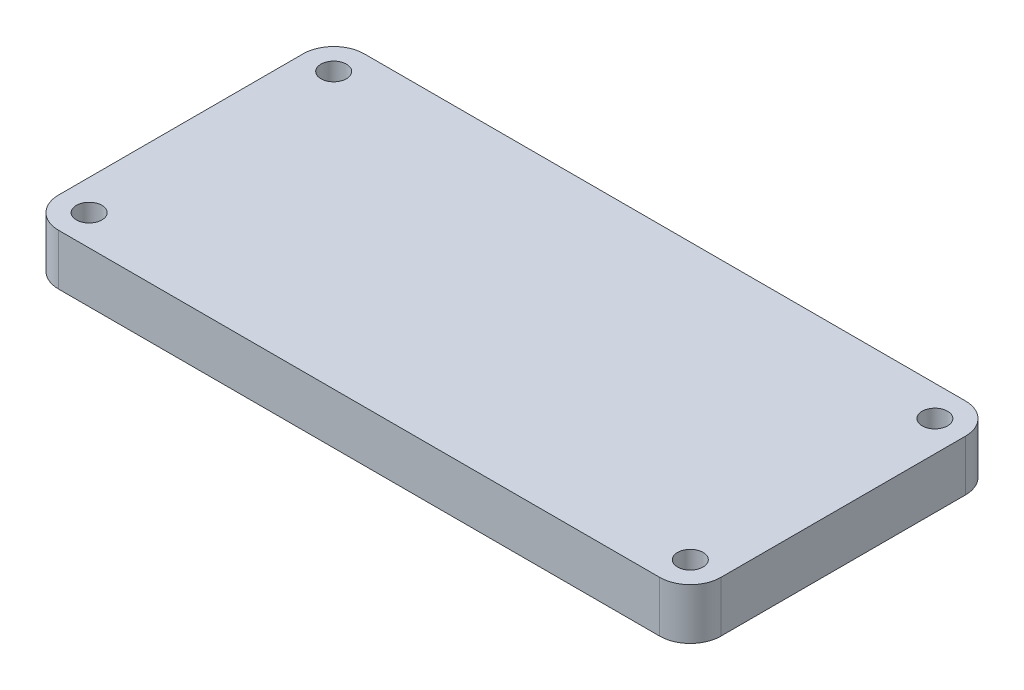
SolidWorks part; units mm, degrees
ref_plane "Front Plane" through (0, 0, 0) normal (0, 0, 1) x (1, 0, 0)
ref_plane "Top Plane" through (0, 0, 0) normal (0, 1, 0) x (1, 0, 0)
ref_plane "Right Plane" through (0, 0, 0) normal (1, 0, 0) x (0, 0, -1)
sketch "Sketch1" plane through (0, 0, 0) normal (0, 1, 0) x (1, 0, 0)
  line L0 (0, 15) -> (0, -15) construction
  line L1 (-29.5, -15) -> (29.5, -15)
  line L2 (-32.5, -12) -> (-32.5, 12)
  line L3 (-29.5, 15) -> (29.5, 15)
  line L4 (32.5, -12) -> (32.5, 12)
  line L5 (-32.5, -15) -> (32.5, 15) construction
  line L6 (-32.5, 15) -> (32.5, -15) construction
  line L7 (-32.5, 0) -> (32.5, 0) construction
  arc A0 (29.5, 15) -> (32.5, 12) centre (29.5, 12) cw
  arc A1 (32.5, -12) -> (29.5, -15) centre (29.5, -12) cw
  arc A2 (-29.5, -15) -> (-32.5, -12) centre (-29.5, -12) cw
  arc A3 (-32.5, 12) -> (-29.5, 15) centre (-29.5, 12) cw
  circle A4 centre (-29.5, 12) radius 1.25
  circle A5 centre (29.5, 12) radius 1.25
  circle A6 centre (29.5, -12) radius 1.25
  circle A7 centre (-29.5, -12) radius 1.25
  point P1 (0, 0)
  dimension "D3" = 3
  dimension "D4" = 2.5
  dimension "D1" = 65
  dimension "D2" = 30
extrude "Boss-Extrude1" add sketch "Sketch1" along normal blind 5
